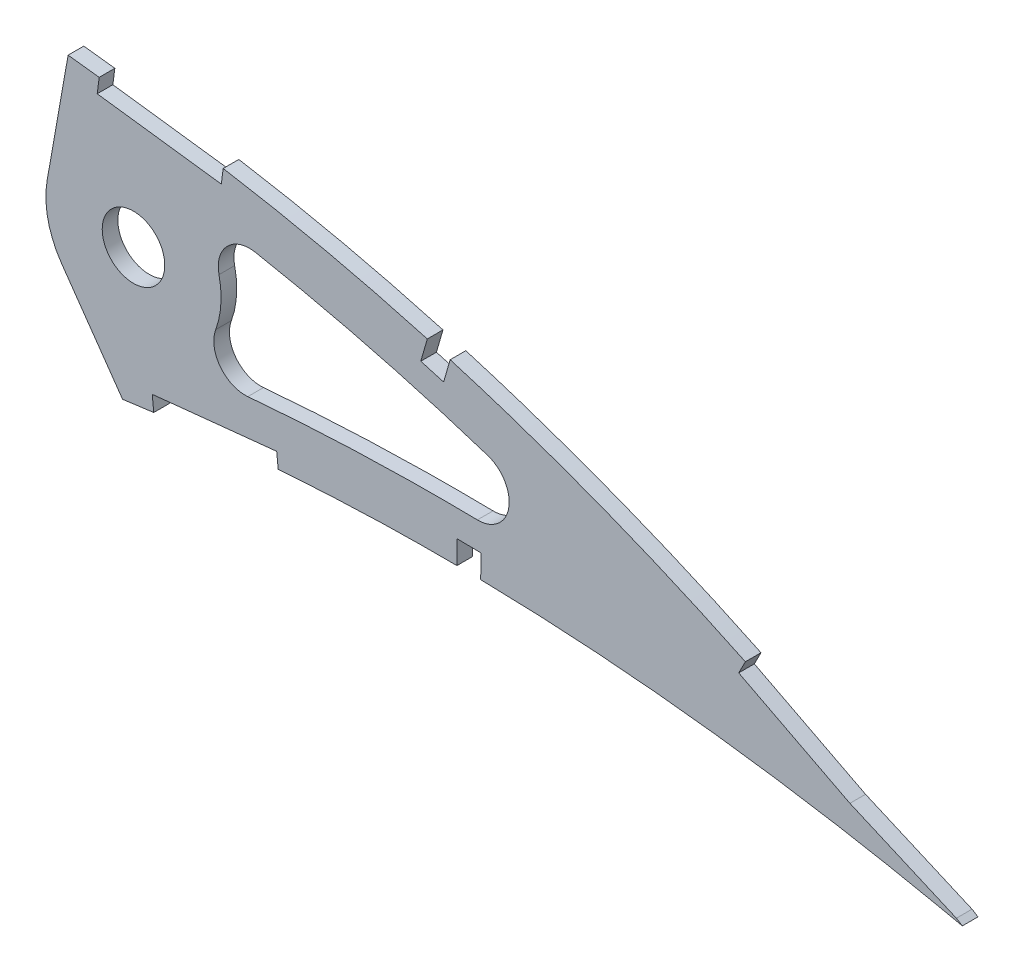
SolidWorks part; units mm, degrees
material "Pine"
ref_plane "Front Plane" through (0, 0, 0) normal (0, 0, 1) x (1, 0, 0)
ref_plane "Top Plane" through (0, 0, 0) normal (0, 1, 0) x (1, 0, 0)
ref_plane "Right Plane" through (0, 0, 0) normal (1, 0, 0) x (0, 0, -1)
curve "Curve1"
  spline degree 3 poles (554.3197, 0.8642, 0) (554.2772, 0.8904, 0) (554.1075, 0.9953, 0) (553.7252, 1.2298, 0) (553.0885, 1.6204, 0) (552.1972, 2.1644, 0) (551.0519, 2.8603, 0) (549.6522, 3.7033, 0) (547.9988, 4.6906, 0) (546.0922, 5.8176, 0) (543.9326, 7.0789, 0) (541.5207, 8.4695, 0) (538.8569, 9.9815, 0) (535.942, 11.6087, 0) (532.7772, 13.3434, 0) (529.3631, 15.1777, 0) (525.7007, 17.1023, 0) (521.7917, 19.109, 0) (517.6366, 21.1866, 0) (513.2374, 23.3265, 0) (508.5956, 25.518, 0) (503.7128, 27.7495, 0) (498.5918, 30.0118, 0) (493.234, 32.2909, 0) (487.6424, 34.577, 0) (481.8195, 36.8569, 0) (475.7686, 39.1203, 0) (469.4922, 41.3526, 0) (462.9949, 43.5439, 0) (456.2798, 45.6802, 0) (449.3518, 47.7496, 0) (442.2149, 49.739, 0) (434.875, 51.6379, 0) (427.3368, 53.4327, 0) (419.6066, 55.1112, 0) (411.6907, 56.6635, 0) (403.5957, 58.0739, 0) (395.344, 59.3415, 0) (387.0683, 60.3958, 0) (378.8096, 61.4299, 0) (370.5633, 62.4014, 0) (362.2161, 63.3317, 0) (353.7762, 64.2156, 0) (345.252, 65.0503, 0) (336.6519, 65.8323, 0) (327.9851, 66.5592, 0) (319.2598, 67.227, 0) (310.4852, 67.8346, 0) (301.6702, 68.3766, 0) (292.8239, 68.8527, 0) (283.9555, 69.2595, 0) (275.0741, 69.5943, 0) (266.1892, 69.8549, 0) (257.3099, 70.039, 0) (248.446, 70.1454, 0) (239.6066, 70.171, 0) (230.8014, 70.1156, 0) (222.0395, 69.9772, 0) (213.3305, 69.7538, 0) (204.6838, 69.4452, 0) (196.1087, 69.0513, 0) (187.6145, 68.5689, 0) (179.2105, 68.0012, 0) (170.9059, 67.3456, 0) (162.7101, 66.6021, 0) (154.6315, 65.7736, 0) (146.6791, 64.8581, 0) (138.8614, 63.858, 0) (131.1871, 62.7754, 0) (123.6647, 61.6096, 0) (116.3022, 60.3641, 0) (109.1077, 59.04, 0) (102.0887, 57.6413, 0) (95.2529, 56.1683, 0) (88.6074, 54.6255, 0) (82.1593, 53.0155, 0) (75.9155, 51.3413, 0) (69.8822, 49.607, 0) (64.0656, 47.8163, 0) (58.4725, 45.9714, 0) (53.107, 44.0792, 0) (47.9758, 42.141, 0) (43.0829, 40.1629, 0) (38.4338, 38.1474, 0) (34.0322, 36.1008, 0) (29.883, 34.0255, 0) (25.9891, 31.9271, 0) (22.3545, 29.809, 0) (18.9827, 27.675, 0) (15.875, 25.5306, 0) (13.0358, 23.3771, 0) (10.4661, 21.22, 0) (8.1674, 19.0625, 0) (6.143, 16.9061, 0) (4.3929, 14.7547, 0) (2.9194, 12.6099, 0) (1.7228, 10.4738, 0) (0.8056, 8.3479, 0) (0.1671, 6.2334, 0) (-0.1824, 4.1334, 0) (-0.2694, 2.0463, 0) (-0.0897, 0.6811, 0) (0, 0, 0) knots 0 0 0 0 0.000254 0.001015 0.002283 0.004057 0.006331 0.009105 0.012374 0.016134 0.02038 0.025106 0.030306 0.035972 0.0421 0.048678 0.055702 0.06316 0.071046 0.07935 0.088063 0.097176 0.106678 0.116562 0.126814 0.137428 0.148394 0.1597 0.171338 0.183298 0.19557 0.208144 0.221012 0.234162 0.247587 0.261277 0.275223 0.289414 0.303771 0.317689 0.331784 0.34604 0.360444 0.374983 0.38964 0.404403 0.419257 0.434187 0.449177 0.464215 0.479284 0.49437 0.509458 0.524532 0.539579 0.554583 0.56953 0.584403 0.599191 0.613877 0.628447 0.642889 0.657186 0.671326 0.685294 0.699078 0.712665 0.726043 0.739198 0.752118 0.764792 0.777208 0.789356 0.801224 0.812804 0.824083 0.835055 0.84571 0.856038 0.866034 0.875689 0.884998 0.893953 0.902553 0.910789 0.918661 0.926166 0.933303 0.940071 0.946475 0.952518 0.958205 0.963547 0.968557 0.97325 0.977651 0.981787 0.985694 0.989415 0.993001 0.996508 1 1 1 1
curve "Curve2"
  spline degree 3 poles (0, 0, 0) (0.1423, -0.672, 0) (0.4277, -2.019, 0) (1.203, -3.9582, 0) (2.2282, -5.8223, 0) (3.5249, -7.6064, 0) (5.0845, -9.31, 0) (6.9036, -10.9348, 0) (8.9803, -12.4801, 0) (11.3119, -13.945, 0) (13.8951, -15.3312, 0) (16.7269, -16.6378, 0) (19.8048, -17.8643, 0) (23.1254, -19.0092, 0) (26.6846, -20.0741, 0) (30.4791, -21.0566, 0) (34.5045, -21.9578, 0) (38.7571, -22.7757, 0) (43.232, -23.5109, 0) (47.9248, -24.1631, 0) (52.8305, -24.7327, 0) (57.9444, -25.2185, 0) (63.2614, -25.6215, 0) (68.7762, -25.942, 0) (74.4834, -26.1811, 0) (80.3777, -26.3377, 0) (86.4531, -26.4144, 0) (92.7043, -26.4123, 0) (99.1251, -26.3308, 0) (105.71, -26.1745, 0) (112.4527, -25.9423, 0) (119.3471, -25.6371, 0) (126.387, -25.2619, 0) (133.5661, -24.818, 0) (140.8781, -24.3074, 0) (148.3166, -23.7341, 0) (155.8748, -23.0997, 0) (163.5462, -22.4077, 0) (171.324, -21.6617, 0) (179.2015, -20.864, 0) (187.1716, -20.0183, 0) (195.2274, -19.1275, 0) (203.3619, -18.1963, 0) (211.5677, -17.2262, 0) (219.8379, -16.223, 0) (228.1647, -15.1885, 0) (236.5412, -14.1266, 0) (244.9597, -13.0425, 0) (253.4125, -11.9359, 0) (261.8924, -10.8148, 0) (270.3912, -9.6781, 0) (278.9016, -8.5319, 0) (287.4156, -7.3796, 0) (295.925, -6.2216, 0) (304.4222, -5.0626, 0) (312.8995, -3.9059, 0) (321.3485, -2.7516, 0) (329.7616, -1.6054, 0) (338.1302, -0.4672, 0) (346.4467, 0.6607, 0) (354.7031, 1.775, 0) (362.8916, 2.8743, 0) (371.0037, 3.9578, 0) (379.0314, 5.0259, 0) (386.8463, 6.0463, 0) (394.4281, 7.0733, 0) (401.8022, 7.9152, 0) (409.0845, 8.6338, 0) (416.2825, 9.2229, 0) (423.3877, 9.6911, 0) (430.3918, 10.0417, 0) (437.2865, 10.2795, 0) (444.0631, 10.4116, 0) (450.7132, 10.4414, 0) (457.2276, 10.3785, 0) (463.598, 10.2277, 0) (469.8153, 9.9961, 0) (475.8709, 9.6912, 0) (481.7563, 9.3216, 0) (487.4626, 8.8925, 0) (492.9818, 8.4141, 0) (498.3055, 7.8933, 0) (503.4254, 7.336, 0) (508.334, 6.7541, 0) (513.0236, 6.1512, 0) (517.4871, 5.5374, 0) (521.7172, 4.9187, 0) (525.7074, 4.3032, 0) (529.4512, 3.6966, 0) (532.9427, 3.1071, 0) (536.1764, 2.5402, 0) (539.1467, 2.0013, 0) (541.8495, 1.4973, 0) (544.2794, 1.0307, 0) (546.4331, 0.6092, 0) (548.3068, 0.2346, 0) (549.8976, -0.0878, 0) (551.2027, -0.3567, 0) (552.2202, -0.5677, 0) (552.948, -0.7211, 0) (553.3854, -0.8124, 0) (553.5798, -0.8538, 0) (553.6283, -0.8642, 0) knots 0 0 0 0 0.003638 0.007293 0.011028 0.014901 0.018963 0.023258 0.027821 0.032679 0.037853 0.043362 0.049215 0.055422 0.061989 0.068918 0.076211 0.083868 0.091887 0.100266 0.109 0.118085 0.127515 0.137285 0.147388 0.157816 0.168563 0.179619 0.190977 0.202627 0.21456 0.226767 0.239236 0.251959 0.264924 0.27812 0.291536 0.30516 0.318981 0.332985 0.347163 0.361499 0.375981 0.390597 0.405333 0.420175 0.43511 0.450124 0.465203 0.480333 0.495501 0.51069 0.525887 0.541078 0.556247 0.571382 0.586466 0.601485 0.616424 0.631269 0.646007 0.660621 0.675098 0.689423 0.703582 0.716908 0.730009 0.742952 0.755726 0.76832 0.780724 0.792927 0.804916 0.816679 0.828204 0.839475 0.850481 0.861208 0.871639 0.881763 0.891564 0.901027 0.910139 0.918884 0.927249 0.935221 0.942785 0.949928 0.956638 0.962904 0.968712 0.974054 0.978918 0.983297 0.98718 0.990561 0.993433 0.995791 0.99763 0.998946 0.999737 1 1 1 1
sketch "Sketch1" plane through (0, 0, 0) normal (0, 0, 1) x (1, 0, 0)
  line L28 (0, 63.5) -> (-23.1981, 63.5) construction
  line L39 (379.9183, -27.3345) -> (379.9183, 27.3345) construction
  line L40 (368.4067, 59.4277) -> (353.2793, 2.9714) construction
  line L41 (537.5238, 0.838) -> (542.0214, -1.9404)
  line L42 (536.8534, -0.838) -> (542.0214, -1.9404)
  circle A0 centre (68.58, 6.35) radius 9.525 construction
  circle A1 centre (246.38, 6.35) radius 9.525 construction
  spline S3 degree 3 poles (0, 0) (0.138, -0.6516) (0.4147, -1.9578) (1.1665, -3.8383) (2.1607, -5.6459) (3.4181, -7.3759) (4.9305, -9.0279) (6.6944, -10.6035) (8.7082, -12.1019) (10.9692, -13.5225) (13.4741, -14.8667) (16.2201, -16.1336) (19.2047, -17.323) (22.4247, -18.4332) (25.8761, -19.4659) (29.5556, -20.4185) (33.4591, -21.2925) (37.5827, -22.0856) (41.9221, -22.7985) (46.4726, -23.431) (51.2297, -23.9833) (56.1887, -24.4544) (61.3446, -24.8452) (66.6923, -25.156) (72.2266, -25.3878) (77.9422, -25.5397) (83.8336, -25.6141) (89.8954, -25.612) (96.1216, -25.533) (102.507, -25.3814) (109.0454, -25.1563) (115.7309, -24.8603) (122.5575, -24.4965) (129.5191, -24.066) (136.6095, -23.5709) (143.8226, -23.015) (151.1518, -22.3997) (158.5908, -21.7287) (166.1329, -21.0053) (173.7717, -20.2318) (181.5003, -19.4118) (189.312, -18.5479) (197.2, -17.6449) (205.1572, -16.7043) (213.1768, -15.7315) (221.2513, -14.7283) (229.374, -13.6986) (237.5374, -12.6473) (245.7341, -11.5743) (253.957, -10.4871) (262.1983, -9.3849) (270.4508, -8.2734) (278.7069, -7.156) (286.9584, -6.033) (295.1983, -4.9092) (303.4187, -3.7876) (311.6117, -2.6683) (319.7698, -1.5568) (327.8848, -0.4531) (335.9493, 0.6407) (343.9556, 1.7212) (351.896, 2.7872) (359.7623, 3.8379) (367.5468, 4.8736) (375.1249, 5.8631) (382.4769, 6.859) (389.6276, 7.6754) (396.6892, 8.3722) (403.6691, 8.9435) (410.559, 9.3975) (417.3509, 9.7374) (424.0367, 9.968) (430.608, 10.0961) (437.0566, 10.1251) (443.3736, 10.064) (449.5509, 9.9178) (455.5799, 9.6932) (461.4521, 9.3976) (467.1591, 9.0391) (472.6925, 8.6231) (478.0445, 8.1591) (483.2068, 7.6541) (488.1716, 7.1138) (492.9315, 6.5494) (497.479, 5.9648) (501.8072, 5.3696) (505.9092, 4.7697) (509.7784, 4.1728) (513.4088, 3.5846) (516.7946, 3.013) (519.9303, 2.4632) (522.8106, 1.9407) (525.4315, 1.4519) (527.7877, 0.9995) (529.8762, 0.5907) (531.6931, 0.2275) (533.2357, -0.0851) (534.5012, -0.3459) (535.4879, -0.5505) (536.1937, -0.6992) (536.6178, -0.7878) (536.8063, -0.828) (536.8534, -0.838) knots 0 0 0 0 0.003638 0.007293 0.011028 0.014901 0.018963 0.023258 0.027821 0.032679 0.037853 0.043362 0.049215 0.055422 0.061989 0.068918 0.076211 0.083868 0.091887 0.100266 0.109 0.118085 0.127515 0.137285 0.147388 0.157816 0.168563 0.179619 0.190977 0.202627 0.21456 0.226767 0.239236 0.251959 0.264924 0.27812 0.291536 0.30516 0.318981 0.332985 0.347163 0.361499 0.375981 0.390597 0.405333 0.420175 0.43511 0.450124 0.465203 0.480333 0.495501 0.51069 0.525887 0.541078 0.556247 0.571382 0.586466 0.601485 0.616424 0.631269 0.646007 0.660621 0.675098 0.689423 0.703582 0.716908 0.730009 0.742952 0.755726 0.76832 0.780724 0.792927 0.804916 0.816679 0.828204 0.839475 0.850481 0.861208 0.871639 0.881763 0.891564 0.901027 0.910139 0.918884 0.927249 0.935221 0.942785 0.949928 0.956638 0.962904 0.968712 0.974054 0.978918 0.983297 0.98718 0.990561 0.993433 0.995791 0.99763 0.998946 0.999737 1 1 1 1
  spline S6 degree 3 poles (537.5238, 0.838) (537.4826, 0.8635) (537.3181, 0.9651) (536.9473, 1.1925) (536.3299, 1.5713) (535.4656, 2.0988) (534.3551, 2.7737) (532.9977, 3.5911) (531.3944, 4.5485) (529.5456, 5.6413) (527.4514, 6.8644) (525.1126, 8.2129) (522.5295, 9.6791) (519.703, 11.2569) (516.6341, 12.9391) (513.3234, 14.7178) (509.772, 16.5841) (505.9814, 18.53) (501.9522, 20.5446) (497.6863, 22.6197) (493.1852, 24.7448) (488.4503, 26.9087) (483.4845, 29.1025) (478.289, 31.3125) (472.8669, 33.5293) (467.2204, 35.7401) (461.3528, 37.9349) (455.2666, 40.0996) (448.9661, 42.2246) (442.4545, 44.296) (435.7364, 46.3028) (428.8157, 48.2319) (421.6983, 50.0733) (414.3885, 51.8137) (406.8926, 53.4414) (399.2165, 54.9466) (391.3668, 56.3143) (383.365, 57.5434) (375.3401, 58.5658) (367.3317, 59.5686) (359.3352, 60.5106) (351.241, 61.4127) (343.0568, 62.2698) (334.7908, 63.0793) (326.4514, 63.8376) (318.0471, 64.5425) (309.5862, 65.19) (301.0775, 65.7792) (292.5296, 66.3048) (283.9513, 66.7665) (275.3516, 67.161) (266.7393, 67.4856) (258.1236, 67.7383) (249.5134, 67.9168) (240.9181, 68.0199) (232.3465, 68.0449) (223.8081, 67.9911) (215.3117, 67.8569) (206.8666, 67.6403) (198.4819, 67.341) (190.1666, 66.959) (181.9298, 66.4913) (173.7804, 65.9407) (165.7275, 65.305) (157.78, 64.584) (149.9461, 63.7807) (142.2347, 62.8929) (134.6539, 61.9231) (127.2121, 60.8733) (119.9176, 59.7429) (112.7783, 58.535) (105.8017, 57.2511) (98.9954, 55.8947) (92.3667, 54.4664) (85.9226, 52.9703) (79.6699, 51.4091) (73.6153, 49.7857) (67.7648, 48.1039) (62.1244, 46.3675) (56.7008, 44.5785) (51.4979, 42.7436) (46.5222, 40.8641) (41.7775, 38.9459) (37.2693, 36.9916) (33.0011, 35.007) (28.9776, 32.9945) (25.2017, 30.9597) (21.6772, 28.9058) (18.4075, 26.8364) (15.394, 24.757) (12.6408, 22.6688) (10.1489, 20.577) (7.9199, 18.4849) (5.9569, 16.3939) (4.2598, 14.3076) (2.831, 12.2278) (1.6706, 10.1565) (0.7812, 8.095) (0.162, 6.0445) (-0.1769, 4.0082) (-0.2612, 1.9843) (-0.087, 0.6604) (0, 0) knots 0 0 0 0 0.000254 0.001015 0.002283 0.004057 0.006331 0.009105 0.012374 0.016134 0.02038 0.025106 0.030306 0.035972 0.0421 0.048678 0.055702 0.06316 0.071046 0.07935 0.088063 0.097176 0.106678 0.116562 0.126814 0.137428 0.148394 0.1597 0.171338 0.183298 0.19557 0.208144 0.221012 0.234162 0.247587 0.261277 0.275223 0.289414 0.303771 0.317689 0.331784 0.34604 0.360444 0.374983 0.38964 0.404403 0.419257 0.434187 0.449177 0.464215 0.479284 0.49437 0.509458 0.524532 0.539579 0.554583 0.56953 0.584403 0.599191 0.613877 0.628447 0.642889 0.657186 0.671326 0.685294 0.699078 0.712665 0.726043 0.739198 0.752118 0.764792 0.777208 0.789356 0.801224 0.812804 0.824083 0.835055 0.84571 0.856038 0.866034 0.875689 0.884998 0.893953 0.902553 0.910789 0.918661 0.926166 0.933303 0.940071 0.946475 0.952518 0.958205 0.963547 0.968557 0.97325 0.977651 0.981787 0.985694 0.989415 0.993001 0.996508 1 1 1 1
  point P10 (78.5929, 16.5948)
  point P11 (227.8303, 32.4941)
  dimension "D2" = 19.05
  dimension "D18" = 177.8
  dimension "D3" = 15
  dimension "D5" = 63.5
  dimension "D7" = 57.15
  dimension "D12" = 57.15
  dimension "D17" = 68.58
extrude "Boss-Extrude1" add sketch "Sketch1" along normal blind 3.175
sketch "Sketch4" plane through (0, 0, 0) normal (0, 0, -1) x (-1, 0, 0)
  line L0 (-356.287, 36.32) -> (-360.5267, 60.365)
  line L1 (-359.2323, 23.0344) -> (-371.5795, 5.4008)
  line L2 (-373.7968, 33.2326) -> (-412.6852, 33.2326)
  circle A0 centre (-373.7968, 33.2326) radius 17.78
  circle A1 centre (-373.7968, 33.2326) radius 6.35
  spline S0 degree 3 poles (-1632.0302, 1674.0962) (-565.4284, -22.6918) (-552.7247, -8.4851) (-536.9473, 1.1925) (-536.3299, 1.5713) (-535.4656, 2.0988) (-534.3551, 2.7737) (-532.9977, 3.5911) (-531.3944, 4.5485) (-529.5456, 5.6413) (-527.4514, 6.8644) (-525.1126, 8.2129) (-522.5295, 9.6791) (-519.703, 11.2569) (-516.6341, 12.9391) (-513.3234, 14.7178) (-509.772, 16.5841) (-505.9814, 18.53) (-501.9522, 20.5446) (-497.6863, 22.6197) (-493.1852, 24.7448) (-488.4503, 26.9087) (-483.4845, 29.1025) (-478.289, 31.3125) (-472.8669, 33.5293) (-467.2204, 35.7401) (-461.3528, 37.9349) (-455.2666, 40.0996) (-448.9661, 42.2246) (-442.4545, 44.296) (-435.7364, 46.3028) (-428.8157, 48.2319) (-421.6983, 50.0733) (-414.3885, 51.8137) (-406.8926, 53.4414) (-399.2165, 54.9466) (-391.3668, 56.3143) (-383.365, 57.5434) (-375.3401, 58.5658) (-367.3317, 59.5686) (-359.3352, 60.5106) (-351.241, 61.4127) (-343.0568, 62.2698) (-334.7908, 63.0793) (-326.4514, 63.8376) (-318.0471, 64.5425) (-309.5862, 65.19) (-301.0775, 65.7792) (-292.5296, 66.3048) (-283.9513, 66.7665) (-275.3516, 67.161) (-266.7393, 67.4856) (-258.1236, 67.7383) (-249.5134, 67.9168) (-240.9181, 68.0199) (-232.3465, 68.0449) (-223.8081, 67.9911) (-215.3117, 67.8569) (-206.8666, 67.6403) (-198.4819, 67.341) (-190.1666, 66.959) (-181.9298, 66.4913) (-173.7804, 65.9407) (-165.7275, 65.305) (-157.78, 64.584) (-149.9461, 63.7807) (-142.2347, 62.8929) (-134.6539, 61.9231) (-127.2121, 60.8733) (-119.9176, 59.7429) (-112.7783, 58.535) (-105.8017, 57.2511) (-98.9954, 55.8947) (-92.3667, 54.4664) (-85.9226, 52.9703) (-79.6699, 51.4091) (-73.6153, 49.7857) (-67.7648, 48.1039) (-62.1244, 46.3675) (-56.7008, 44.5785) (-51.4979, 42.7436) (-46.5222, 40.8641) (-41.7775, 38.9459) (-37.2693, 36.9916) (-33.0011, 35.007) (-28.9776, 32.9945) (-25.2017, 30.9597) (-21.6772, 28.9058) (-18.4075, 26.8364) (-15.394, 24.757) (-12.6408, 22.6688) (-10.1489, 20.577) (-7.9199, 18.4849) (-5.9569, 16.3939) (-4.2598, 14.3076) (-2.831, 12.2278) (-1.6706, 10.1565) (-0.7812, 8.095) (-0.162, 6.0445) (0.1769, 4.0082) (1.1707, -19.8347) (-66.7598, -38.6935) (1990.434, -189.4699) knots -0.094882 -0.094882 -0.094882 -0.094882 0.000254 0.001015 0.002283 0.004057 0.006331 0.009105 0.012374 0.016134 0.02038 0.025106 0.030306 0.035972 0.0421 0.048678 0.055702 0.06316 0.071046 0.07935 0.088063 0.097176 0.106678 0.116562 0.126814 0.137428 0.148394 0.1597 0.171338 0.183298 0.19557 0.208144 0.221012 0.234162 0.247587 0.261277 0.275223 0.289414 0.303771 0.317689 0.331784 0.34604 0.360444 0.374983 0.38964 0.404403 0.419257 0.434187 0.449177 0.464215 0.479284 0.49437 0.509458 0.524532 0.539579 0.554583 0.56953 0.584403 0.599191 0.613877 0.628447 0.642889 0.657186 0.671326 0.685294 0.699078 0.712665 0.726043 0.739198 0.752118 0.764792 0.777208 0.789356 0.801224 0.812804 0.824083 0.835055 0.84571 0.856038 0.866034 0.875689 0.884998 0.893953 0.902553 0.910789 0.918661 0.926166 0.933303 0.940071 0.946475 0.952518 0.958205 0.963547 0.968557 0.97325 0.977651 0.981787 0.985694 0.989415 0.993001 0.996508 1.114113 1.114113 1.114113 1.114113 only from (-537.5238, 0.838) to (0, 0) construction
  spline S1 degree 3 poles (1940.1203, -483.4322) (-49.9299, 58.7424) (7.7069, 18.357) (-1.1665, -3.8383) (-2.1607, -5.6459) (-3.4181, -7.3759) (-4.9305, -9.0279) (-6.6944, -10.6035) (-8.7082, -12.1019) (-10.9692, -13.5225) (-13.4741, -14.8667) (-16.2201, -16.1336) (-19.2047, -17.323) (-22.4247, -18.4332) (-25.8761, -19.4659) (-29.5556, -20.4185) (-33.4591, -21.2925) (-37.5827, -22.0856) (-41.9221, -22.7985) (-46.4726, -23.431) (-51.2297, -23.9833) (-56.1887, -24.4544) (-61.3446, -24.8452) (-66.6923, -25.156) (-72.2266, -25.3878) (-77.9422, -25.5397) (-83.8336, -25.6141) (-89.8954, -25.612) (-96.1216, -25.533) (-102.507, -25.3814) (-109.0454, -25.1563) (-115.7309, -24.8603) (-122.5575, -24.4965) (-129.5191, -24.066) (-136.6095, -23.5709) (-143.8226, -23.015) (-151.1518, -22.3997) (-158.5908, -21.7287) (-166.1329, -21.0053) (-173.7717, -20.2318) (-181.5003, -19.4118) (-189.312, -18.5479) (-197.2, -17.6449) (-205.1572, -16.7043) (-213.1768, -15.7315) (-221.2513, -14.7283) (-229.374, -13.6986) (-237.5374, -12.6473) (-245.7341, -11.5743) (-253.957, -10.4871) (-262.1983, -9.3849) (-270.4508, -8.2734) (-278.7069, -7.156) (-286.9584, -6.033) (-295.1983, -4.9092) (-303.4187, -3.7876) (-311.6117, -2.6683) (-319.7698, -1.5568) (-327.8848, -0.4531) (-335.9493, 0.6407) (-343.9556, 1.7212) (-351.896, 2.7872) (-359.7623, 3.8379) (-367.5468, 4.8736) (-375.1249, 5.8631) (-382.4769, 6.859) (-389.6276, 7.6754) (-396.6892, 8.3722) (-403.6691, 8.9435) (-410.559, 9.3975) (-417.3509, 9.7374) (-424.0367, 9.968) (-430.608, 10.0961) (-437.0566, 10.1251) (-443.3736, 10.064) (-449.5509, 9.9178) (-455.5799, 9.6932) (-461.4521, 9.3976) (-467.1591, 9.0391) (-472.6925, 8.6231) (-478.0445, 8.1591) (-483.2068, 7.6541) (-488.1716, 7.1138) (-492.9315, 6.5494) (-497.479, 5.9648) (-501.8072, 5.3696) (-505.9092, 4.7697) (-509.7784, 4.1728) (-513.4088, 3.5846) (-516.7946, 3.013) (-519.9303, 2.4632) (-522.8106, 1.9407) (-525.4315, 1.4519) (-527.7877, 0.9995) (-529.8762, 0.5907) (-531.6931, 0.2275) (-533.2357, -0.0851) (-534.5012, -0.3459) (-535.4879, -0.5505) (-536.1937, -0.6992) (-552.4366, -4.0895) (-567.1821, -13.3973) (-997.8539, 1944.6618) knots -0.119141 -0.119141 -0.119141 -0.119141 0.003638 0.007293 0.011028 0.014901 0.018963 0.023258 0.027821 0.032679 0.037853 0.043362 0.049215 0.055422 0.061989 0.068918 0.076211 0.083868 0.091887 0.100266 0.109 0.118085 0.127515 0.137285 0.147388 0.157816 0.168563 0.179619 0.190977 0.202627 0.21456 0.226767 0.239236 0.251959 0.264924 0.27812 0.291536 0.30516 0.318981 0.332985 0.347163 0.361499 0.375981 0.390597 0.405333 0.420175 0.43511 0.450124 0.465203 0.480333 0.495501 0.51069 0.525887 0.541078 0.556247 0.571382 0.586466 0.601485 0.616424 0.631269 0.646007 0.660621 0.675098 0.689423 0.703582 0.716908 0.730009 0.742952 0.755726 0.76832 0.780724 0.792927 0.804916 0.816679 0.828204 0.839475 0.850481 0.861208 0.871639 0.881763 0.891564 0.901027 0.910139 0.918884 0.927249 0.935221 0.942785 0.949928 0.956638 0.962904 0.968712 0.974054 0.978918 0.983297 0.98718 0.990561 0.993433 0.995791 0.99763 0.998946 0.999737 1.088404 1.088404 1.088404 1.088404 only from (0, 0) to (-536.8534, -0.838) construction
  spline S2 degree 3 poles (-537.5238, 0.838) (-537.4826, 0.8635) (-537.3181, 0.9651) (-536.9473, 1.1925) (-536.3299, 1.5713) (-535.4656, 2.0988) (-534.3551, 2.7737) (-532.9977, 3.5911) (-531.3944, 4.5485) (-529.5456, 5.6413) (-527.4514, 6.8644) (-525.1126, 8.2129) (-522.5295, 9.6791) (-519.703, 11.2569) (-516.6341, 12.9391) (-513.3234, 14.7178) (-509.772, 16.5841) (-505.9814, 18.53) (-501.9522, 20.5446) (-497.6863, 22.6197) (-493.1852, 24.7448) (-488.4503, 26.9087) (-483.4845, 29.1025) (-478.289, 31.3125) (-472.8669, 33.5293) (-467.2204, 35.7401) (-461.3528, 37.9349) (-455.2666, 40.0996) (-448.9661, 42.2246) (-442.4545, 44.296) (-435.7364, 46.3028) (-428.8157, 48.2319) (-421.6983, 50.0733) (-414.3885, 51.8137) (-406.8926, 53.4414) (-399.2165, 54.9466) (-391.3668, 56.3143) (-383.365, 57.5434) (-375.3401, 58.5658) (-367.3317, 59.5686) (-359.3352, 60.5106) (-351.241, 61.4127) (-343.0568, 62.2698) (-334.7908, 63.0793) (-326.4514, 63.8376) (-318.0471, 64.5425) (-309.5862, 65.19) (-301.0775, 65.7792) (-292.5296, 66.3048) (-283.9513, 66.7665) (-275.3516, 67.161) (-266.7393, 67.4856) (-258.1236, 67.7383) (-249.5134, 67.9168) (-240.9181, 68.0199) (-232.3465, 68.0449) (-223.8081, 67.9911) (-215.3117, 67.8569) (-206.8666, 67.6403) (-198.4819, 67.341) (-190.1666, 66.959) (-181.9298, 66.4913) (-173.7804, 65.9407) (-165.7275, 65.305) (-157.78, 64.584) (-149.9461, 63.7807) (-142.2347, 62.8929) (-134.6539, 61.9231) (-127.2121, 60.8733) (-119.9176, 59.7429) (-112.7783, 58.535) (-105.8017, 57.2511) (-98.9954, 55.8947) (-92.3667, 54.4664) (-85.9226, 52.9703) (-79.6699, 51.4091) (-73.6153, 49.7857) (-67.7648, 48.1039) (-62.1244, 46.3675) (-56.7008, 44.5785) (-51.4979, 42.7436) (-46.5222, 40.8641) (-41.7775, 38.9459) (-37.2693, 36.9916) (-33.0011, 35.007) (-28.9776, 32.9945) (-25.2017, 30.9597) (-21.6772, 28.9058) (-18.4075, 26.8364) (-15.394, 24.757) (-12.6408, 22.6688) (-10.1489, 20.577) (-7.9199, 18.4849) (-5.9569, 16.3939) (-4.2598, 14.3076) (-2.831, 12.2278) (-1.6706, 10.1565) (-0.7812, 8.095) (-0.162, 6.0445) (0.1769, 4.0082) (0.2612, 1.9843) (0.087, 0.6604) (0, 0) knots 0 0 0 0 0.000254 0.001015 0.002283 0.004057 0.006331 0.009105 0.012374 0.016134 0.02038 0.025106 0.030306 0.035972 0.0421 0.048678 0.055702 0.06316 0.071046 0.07935 0.088063 0.097176 0.106678 0.116562 0.126814 0.137428 0.148394 0.1597 0.171338 0.183298 0.19557 0.208144 0.221012 0.234162 0.247587 0.261277 0.275223 0.289414 0.303771 0.317689 0.331784 0.34604 0.360444 0.374983 0.38964 0.404403 0.419257 0.434187 0.449177 0.464215 0.479284 0.49437 0.509458 0.524532 0.539579 0.554583 0.56953 0.584403 0.599191 0.613877 0.628447 0.642889 0.657186 0.671326 0.685294 0.699078 0.712665 0.726043 0.739198 0.752118 0.764792 0.777208 0.789356 0.801224 0.812804 0.824083 0.835055 0.84571 0.856038 0.866034 0.875689 0.884998 0.893953 0.902553 0.910789 0.918661 0.926166 0.933303 0.940071 0.946475 0.952518 0.958205 0.963547 0.968557 0.97325 0.977651 0.981787 0.985694 0.989415 0.993001 0.996508 1 1 1 1
  spline S3 degree 3 poles (0, 0) (-0.138, -0.6516) (-0.4147, -1.9578) (-1.1665, -3.8383) (-2.1607, -5.6459) (-3.4181, -7.3759) (-4.9305, -9.0279) (-6.6944, -10.6035) (-8.7082, -12.1019) (-10.9692, -13.5225) (-13.4741, -14.8667) (-16.2201, -16.1336) (-19.2047, -17.323) (-22.4247, -18.4332) (-25.8761, -19.4659) (-29.5556, -20.4185) (-33.4591, -21.2925) (-37.5827, -22.0856) (-41.9221, -22.7985) (-46.4726, -23.431) (-51.2297, -23.9833) (-56.1887, -24.4544) (-61.3446, -24.8452) (-66.6923, -25.156) (-72.2266, -25.3878) (-77.9422, -25.5397) (-83.8336, -25.6141) (-89.8954, -25.612) (-96.1216, -25.533) (-102.507, -25.3814) (-109.0454, -25.1563) (-115.7309, -24.8603) (-122.5575, -24.4965) (-129.5191, -24.066) (-136.6095, -23.5709) (-143.8226, -23.015) (-151.1518, -22.3997) (-158.5908, -21.7287) (-166.1329, -21.0053) (-173.7717, -20.2318) (-181.5003, -19.4118) (-189.312, -18.5479) (-197.2, -17.6449) (-205.1572, -16.7043) (-213.1768, -15.7315) (-221.2513, -14.7283) (-229.374, -13.6986) (-237.5374, -12.6473) (-245.7341, -11.5743) (-253.957, -10.4871) (-262.1983, -9.3849) (-270.4508, -8.2734) (-278.7069, -7.156) (-286.9584, -6.033) (-295.1983, -4.9092) (-303.4187, -3.7876) (-311.6117, -2.6683) (-319.7698, -1.5568) (-327.8848, -0.4531) (-335.9493, 0.6407) (-343.9556, 1.7212) (-351.896, 2.7872) (-359.7623, 3.8379) (-367.5468, 4.8736) (-375.1249, 5.8631) (-382.4769, 6.859) (-389.6276, 7.6754) (-396.6892, 8.3722) (-403.6691, 8.9435) (-410.559, 9.3975) (-417.3509, 9.7374) (-424.0367, 9.968) (-430.608, 10.0961) (-437.0566, 10.1251) (-443.3736, 10.064) (-449.5509, 9.9178) (-455.5799, 9.6932) (-461.4521, 9.3976) (-467.1591, 9.0391) (-472.6925, 8.6231) (-478.0445, 8.1591) (-483.2068, 7.6541) (-488.1716, 7.1138) (-492.9315, 6.5494) (-497.479, 5.9648) (-501.8072, 5.3696) (-505.9092, 4.7697) (-509.7784, 4.1728) (-513.4088, 3.5846) (-516.7946, 3.013) (-519.9303, 2.4632) (-522.8106, 1.9407) (-525.4315, 1.4519) (-527.7877, 0.9995) (-529.8762, 0.5907) (-531.6931, 0.2275) (-533.2357, -0.0851) (-534.5012, -0.3459) (-535.4879, -0.5505) (-536.1937, -0.6992) (-536.6178, -0.7878) (-536.8063, -0.828) (-536.8534, -0.838) knots 0 0 0 0 0.003638 0.007293 0.011028 0.014901 0.018963 0.023258 0.027821 0.032679 0.037853 0.043362 0.049215 0.055422 0.061989 0.068918 0.076211 0.083868 0.091887 0.100266 0.109 0.118085 0.127515 0.137285 0.147388 0.157816 0.168563 0.179619 0.190977 0.202627 0.21456 0.226767 0.239236 0.251959 0.264924 0.27812 0.291536 0.30516 0.318981 0.332985 0.347163 0.361499 0.375981 0.390597 0.405333 0.420175 0.43511 0.450124 0.465203 0.480333 0.495501 0.51069 0.525887 0.541078 0.556247 0.571382 0.586466 0.601485 0.616424 0.631269 0.646007 0.660621 0.675098 0.689423 0.703582 0.716908 0.730009 0.742952 0.755726 0.76832 0.780724 0.792927 0.804916 0.816679 0.828204 0.839475 0.850481 0.861208 0.871639 0.881763 0.891564 0.901027 0.910139 0.918884 0.927249 0.935221 0.942785 0.949928 0.956638 0.962904 0.968712 0.974054 0.978918 0.983297 0.98718 0.990561 0.993433 0.995791 0.99763 0.998946 0.999737 1 1 1 1
  spline S4 degree 1 poles (-532.1841, -7.8057) (-10.0219, 1.7185) knots 0 0 1 1 construction
  spline S5 degree 1 poles (-10.0219, 1.7185) (-538.9729, 9.0984) knots 0 0 1 1 construction
  spline S6 degree 3 poles (-532.1841, -7.8057) (-532.035, -7.7136) (-531.7436, -7.5345) (-531.1023, -7.1412) (-530.0303, -6.4862) (-527.85, -5.1645) (-523.4829, -2.5651) (-514.6678, 2.5066) (-496.7411, 12.095) (-470.3238, 24.1396) (-442.9694, 33.791) (-420.6386, 39.9785) (-406.5149, 43.1961) (-395.1531, 45.3637) (-386.5599, 46.8051) (-378.0384, 47.9972) (-369.1749, 49.1011) (-360.4166, 50.162) (-348.6799, 51.484) (-328.147, 53.5808) (-298.749, 55.9238) (-263.4315, 57.6196) (-228.1119, 58.0844) (-192.8506, 57.171) (-157.7356, 54.6709) (-128.7085, 51.0365) (-105.7459, 46.987) (-88.7097, 43.306) (-71.9299, 38.8842) (-58.261, 34.4734) (-47.6305, 30.4115) (-39.8596, 27.063) (-32.3674, 23.3733) (-25.2794, 19.2928) (-18.8179, 14.7781) (-14.319, 10.6534) (-11.7187, 7.3378) (-10.6606, 5.4268) (-10.2382, 4.2645) (-10.0884, 3.6968) (-10.0101, 3.295) (-9.9553, 2.8496) (-9.9432, 2.5723) (-9.9453, 2.4518) (-9.9493, 2.3713) (-9.9688, 2.1598) (-9.9949, 1.9339) (-10.0132, 1.7875) (-10.0219, 1.7185) knots 0 0 0 0 0.000976 0.001952 0.003903 0.007807 0.015613 0.031226 0.062452 0.124904 0.187357 0.218583 0.249809 0.265422 0.281035 0.296648 0.312261 0.327874 0.343487 0.374713 0.437166 0.499618 0.56207 0.624522 0.686974 0.749427 0.780653 0.811879 0.843105 0.874331 0.889944 0.905557 0.92117 0.936783 0.952396 0.968009 0.975816 0.983623 0.987526 0.989477 0.991429 0.993381 0.995332 0.996308 0.997284 0.99826 0.998748 0.999236 0.999236 0.999236 0.999236
  spline S7 degree 3 poles (-10.0219, 1.7185) (-10.0361, 1.6529) (-10.0665, 1.5144) (-10.1157, 1.2979) (-10.1669, 1.0931) (-10.1938, 1.0009) (-10.2267, 0.9008) (-10.3197, 0.6625) (-10.5705, 0.1458) (-10.9157, -0.4199) (-11.7404, -1.469) (-13.2635, -2.8937) (-16.5705, -5.1355) (-21.8641, -7.6046) (-29.0738, -9.8943) (-36.7462, -11.652) (-44.6834, -12.9788) (-52.7844, -13.9626) (-63.7273, -14.8945) (-77.583, -15.4719) (-94.3476, -15.4772) (-111.1866, -14.9569) (-133.6938, -13.7131) (-161.8825, -11.3422) (-195.7357, -7.6685) (-229.6092, -3.472) (-263.4966, 1.0208) (-297.4142, 5.6457) (-325.6956, 9.51) (-345.5133, 12.184) (-356.8358, 13.6973) (-363.916, 14.6412) (-369.594, 15.387) (-373.812, 15.9419) (-378.0525, 16.5127) (-382.4211, 17.0728) (-386.7861, 17.5755) (-392.5828, 18.1876) (-402.7738, 19.115) (-417.3468, 20.0031) (-440.7096, 20.5101) (-469.8877, 19.4483) (-498.8731, 16.2543) (-518.9745, 12.9996) (-528.9918, 11.1265) (-533.6061, 10.2081) (-535.7587, 9.7686) (-536.8071, 9.5524) (-537.7352, 9.359) (-538.3978, 9.2197) (-538.786, 9.1383) (-538.9729, 9.0984) knots 0.000796 0.000796 0.000796 0.000796 0.001284 0.001772 0.002748 0.003724 0.004699 0.006651 0.008603 0.012506 0.016409 0.024215 0.032021 0.047634 0.063247 0.078859 0.094472 0.110084 0.125697 0.156922 0.188147 0.219372 0.250597 0.313047 0.375498 0.437948 0.500398 0.562848 0.625299 0.656524 0.672136 0.687749 0.695555 0.703361 0.711168 0.718974 0.72678 0.734587 0.750199 0.781424 0.812649 0.8751 0.93755 0.968775 0.984387 0.992194 0.994145 0.996097 0.998048 0.999024 1 1 1 1
  dimension "D1" = 35.56
  dimension "D3" = 80
  dimension "D4" = 55
  dimension "D2" = 10.16
extrude "Cut-Extrude2" cut sketch "Sketch4" against normal through all
sketch "Sketch5" plane through (0, 0, 3.175) normal (0, 0, 1) x (1, 0, 0)
  line L1 (392.0264, 56.3907) -> (366.8423, 59.6743)
  line L3 (391.616, 53.2426) -> (392.0264, 56.3907)
  line L5 (402.8557, 11.8924) -> (377.5967, 9.2826)
  line L7 (438.0805, 45.6488) -> (433.4452, 46.9876)
  line L9 (436.7417, 41.0136) -> (438.0805, 45.6488)
  line L11 (403.1819, 8.735) -> (402.8557, 11.8924)
  line L13 (444.3268, 14.772) -> (439.5023, 14.8365)
  line L15 (444.2624, 9.9476) -> (444.3268, 14.772)
  line L17 (520.5603, 11.064) -> (498.0773, 22.6526)
  line L19 (543.7622, 0.9878) -> (520.5603, 11.064)
  line L21 (377.9229, 6.1253) -> (403.1819, 8.735)
  line L23 (366.4319, 56.5263) -> (391.616, 53.2426)
  line L25 (439.4379, 10.012) -> (444.2624, 9.9476)
  line L27 (432.1064, 42.3524) -> (436.7417, 41.0136)
  line L29 (496.6227, 19.8304) -> (519.1997, 8.1935)
  line L31 (519.1997, 8.1935) -> (542.4974, -1.9245)
  line L33 (542.4974, -1.9245) -> (543.7622, 0.9878)
  line L35 (433.4452, 46.9876) -> (432.1064, 42.3524)
  line L37 (498.0773, 22.6526) -> (496.6227, 19.8304)
  line L39 (439.5023, 14.8365) -> (439.4379, 10.012)
  line L41 (377.5967, 9.2826) -> (377.9229, 6.1253)
  line L43 (366.8423, 59.6743) -> (366.4319, 56.5263)
extrude "Cut-Extrude3" cut sketch "Sketch5" against normal blind 7.62
fillet "Fillet1" radius 6.35 3 edges at (483.9453, 17.7821, 1.5875) (380.7081, 16.8508, 1.5875) (385.0563, 46.9931, 1.5875)
